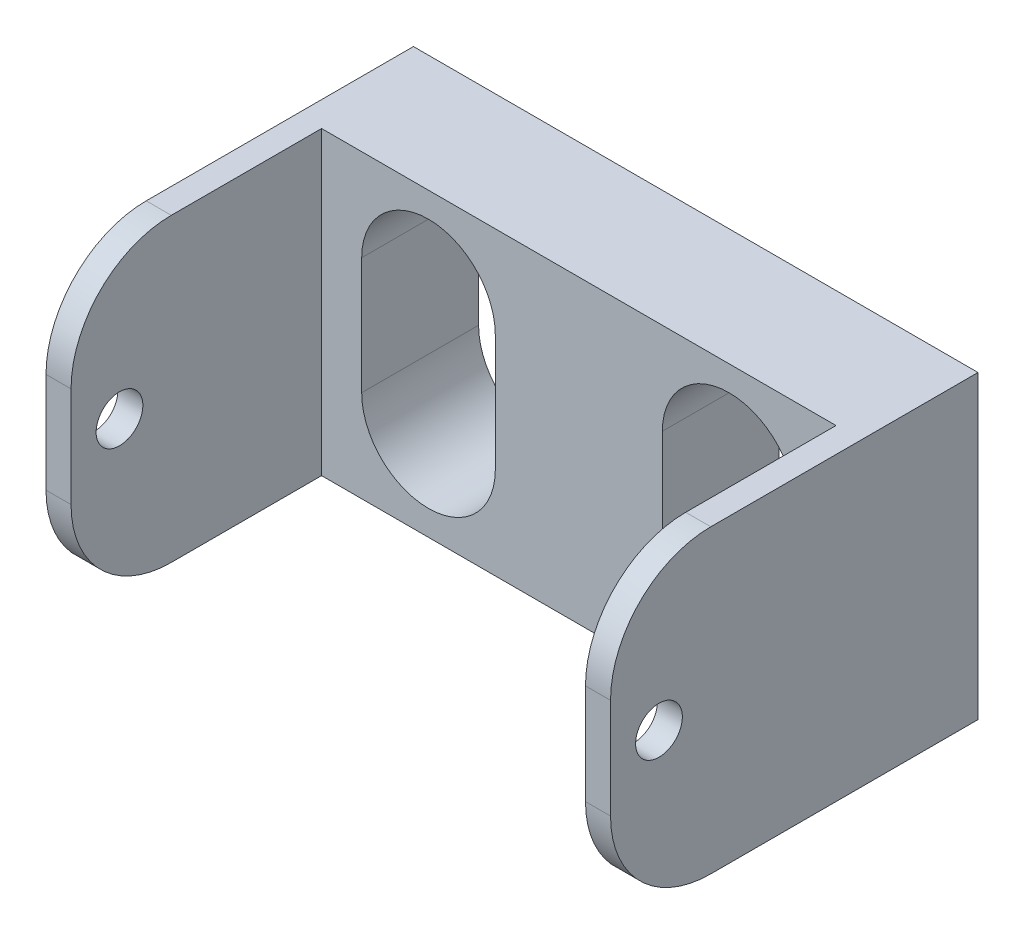
SolidWorks part; units mm, degrees
ref_plane "Front Plane" through (0, 0, 0) normal (0, 0, 1) x (1, 0, 0)
ref_plane "Top Plane" through (0, 0, 0) normal (0, 1, 0) x (1, 0, 0)
ref_plane "Right Plane" through (0, 0, 0) normal (1, 0, 0) x (0, 0, -1)
sketch "Sketch1" plane through (0, 0, 0) normal (0, 0, 1) x (1, 0, 0)
  line L0 (-9, 3.5) -> (-9, -3.5) construction
  line L1 (-16.9, -9) -> (16.9, -9)
  line L2 (-16.9, -9) -> (-16.9, 9)
  line L3 (-16.9, 9) -> (16.9, 9)
  line L4 (16.9, -9) -> (16.9, 9)
  line L5 (-16.9, -9) -> (16.9, 9) construction
  line L6 (-16.9, 9) -> (16.9, -9) construction
  line L7 (-5, 3.5) -> (-5, -3.5)
  line L8 (-13, 3.5) -> (-13, -3.5)
  line L9 (9, 3.5) -> (9, -3.5) construction
  line L10 (13, 3.5) -> (13, -3.5)
  line L11 (5, 3.5) -> (5, -3.5)
  arc A0 (-5, 3.5) -> (-13, 3.5) centre (-9, 3.5) ccw
  arc A1 (-13, -3.5) -> (-5, -3.5) centre (-9, -3.5) ccw
  arc A2 (13, 3.5) -> (5, 3.5) centre (9, 3.5) ccw
  arc A3 (5, -3.5) -> (13, -3.5) centre (9, -3.5) ccw
  point P0 (0, 0)
  point P8 (-9, 0)
  point P15 (9, 0)
  dimension "D1" = 33.8
  dimension "D2" = 18
  dimension "D3" = 8
  dimension "D4" = 7
  dimension "D5" = 8
  dimension "D6" = 7
  dimension "D7" = 10
  dimension "D8" = 5
extrude "Boss-Extrude1" add sketch "Sketch1" along normal blind 7
sketch "Sketch2" plane through (0, 0, 7) normal (0, 0, 1) x (1, 0, 0)
  line L0 (-16.9, -9) -> (16.9, -9) construction
  line L1 (-16.9, 9) -> (-15.4, 9)
  line L2 (-16.9, 9) -> (-16.9, -9)
  line L3 (-16.9, -9) -> (-15.4, -9)
  line L4 (-15.4, 9) -> (-15.4, -9)
  line L6 (16.9, 9) -> (15.4, 9)
  line L7 (16.9, 9) -> (16.9, -9)
  line L8 (16.9, -9) -> (15.4, -9)
  line L9 (15.4, 9) -> (15.4, -9)
  dimension "D1" = 1.5
  dimension "D2" = 1.5
extrude "Boss-Extrude2" add sketch "Sketch2" along normal blind 15
sketch "Sketch3" plane through (16.9, 0, 0) normal (1, 0, 0) x (0, 0, -1)
  line L0 (-22, -9) -> (-22, 9) construction
  circle A0 centre (-19.1, 0) radius 1.4
  point P2 (-22, 0)
  dimension "D1" = 2.8
  dimension "D2" = 2.9
extrude "Cut-Extrude1" cut sketch "Sketch3" against normal through all
fillet "Fillet1" radius 6 4 edges at (16.15, -9, 22) (-16.15, -9, 22) (-16.15, 9, 22) (16.15, 9, 22)
